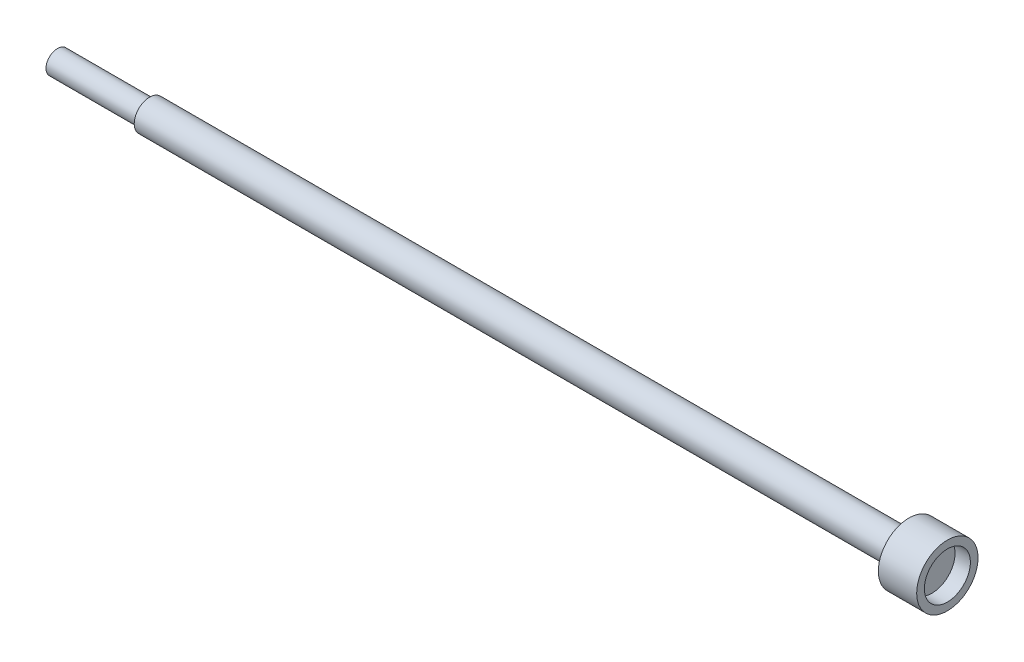
SolidWorks part; units mm, degrees
material "Plain Carbon Steel"
ref_plane "Front Plane" through (0, 0, 0) normal (0, 0, 1) x (1, 0, 0)
ref_plane "Top Plane" through (0, 0, 0) normal (0, 1, 0) x (1, 0, 0)
ref_plane "Right Plane" through (0, 0, 0) normal (1, 0, 0) x (0, 0, -1)
sketch "Sketch2" plane through (0, 0, 0) normal (0, 1, 0) x (1, 0, 0)
  line L0 (-723.9, 0) -> (0, 0)
  line L1 (-723.9, 0) -> (-723.9, 9.525)
  line L2 (-723.9, 9.525) -> (-647.7, 9.525)
  line L3 (-647.7, 9.525) -> (-647.7, 12.7)
  line L4 (-647.7, 12.7) -> (-19.05, 12.7)
  line L5 (0, 19.05) -> (0, 0) construction
  line L9 (-19.05, 12.7) -> (-19.05, 25.4)
  line L10 (-19.05, 25.4) -> (12.7, 25.4)
  line L11 (12.7, 25.4) -> (12.7, 19.05)
  line L12 (12.7, 19.05) -> (0, 19.05)
  point P4 (0, 0)
  dimension "D1" = 723.9
  dimension "D2" = 9.525
  dimension "D3" = 19.05
  dimension "D4" = 76.2
  dimension "D5" = 31.75
  dimension "D6" = 25.4
  dimension "D7" = 19.05
  dimension "D8" = 12.7
revolve "Revolve1" add sketch "Sketch2" angle 360 about L0
sketch "Sketch3" plane through (0, 0, 0) normal (0, 1, 0) x (1, 0, 0)
  line L0 (-19.05, 12.7) -> (-647.7, 12.7) construction
  line L5 (-723.9, 0) -> (-411.48, 0) construction
  line L6 (-723.9, 9.525) -> (-723.9, -9.525) construction
  line L7 (-411.48, 0) -> (-411.48, 11.1125) construction
  line L9 (-424.18, 9.525) -> (-398.78, 9.525)
  line L10 (-424.18, 9.525) -> (-424.18, 12.7)
  line L11 (-424.18, 12.7) -> (-398.78, 12.7)
  line L12 (-398.78, 9.525) -> (-398.78, 12.7)
  line L13 (-424.18, 9.525) -> (-398.78, 12.7) construction
  line L14 (-424.18, 12.7) -> (-398.78, 9.525) construction
  point P10 (0, 0)
  point P11 (0, 0)
  dimension "D1" = 312.42
  dimension "D2" = 25.4
  dimension "D3" = 3.175
extrude "Cut-Extrude1" cut sketch "Sketch3" against normal through all both and the other way through all
